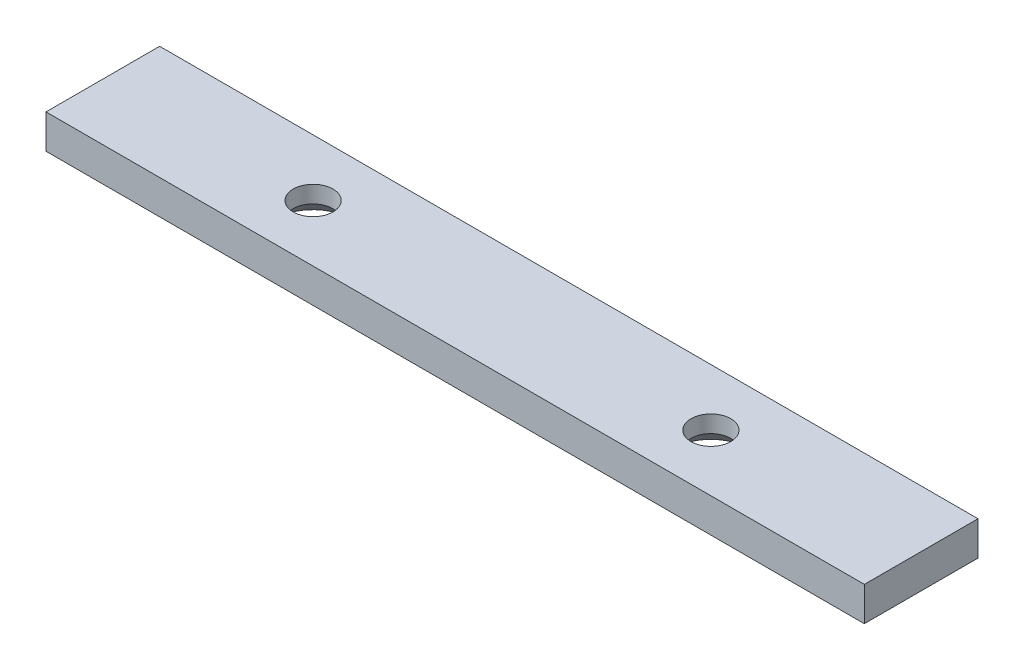
SolidWorks part; units mm, degrees
ref_plane "Front Plane" through (0, 0, 0) normal (0, 0, 1) x (1, 0, 0)
ref_plane "Top Plane" through (0, 0, 0) normal (0, 1, 0) x (1, 0, 0)
ref_plane "Right Plane" through (0, 0, 0) normal (1, 0, 0) x (0, 0, -1)
sketch "Sketch1" plane through (0, 0, 0) normal (0, 1, 0) x (1, 0, 0)
  line L0 (0, 0) -> (-70, 0) construction
  line L1 (-70, 0) -> (-35, 0) construction
  line L2 (37, 10) -> (-107, 10)
  line L3 (37, 10) -> (37, -10)
  line L4 (37, -10) -> (-107, -10)
  line L5 (-107, 10) -> (-107, -10)
  line L6 (37, 10) -> (-107, -10) construction
  line L7 (37, -10) -> (-107, 10) construction
  circle A0 centre (0, 0) radius 3.5
  circle A1 centre (-70, 0) radius 3.5
  point P5 (-35, 0)
  dimension "D2" = 7
  dimension "D3" = 7
  dimension "D1" = 70
  dimension "D4" = 144
  dimension "D5" = 20
extrude "Boss-Extrude2" add sketch "Sketch1" along normal blind 6
chamfer "Chamfer3" distance 3 angle 45 2 edges at (-70, 0, 3.5) (0, 0, 3.5)
